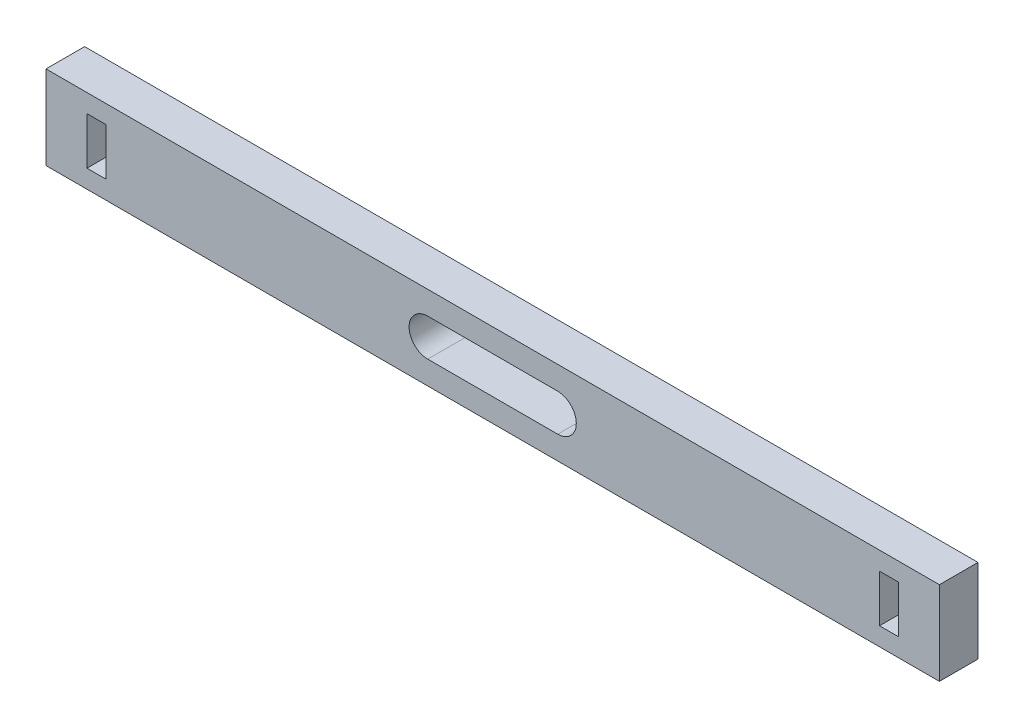
SolidWorks part; units mm, degrees
ref_plane "정면" through (0, 0, 0) normal (0, 0, 1) x (1, 0, 0)
ref_plane "윗면" through (0, 0, 0) normal (0, 1, 0) x (1, 0, 0)
ref_plane "우측면" through (0, 0, 0) normal (1, 0, 0) x (0, 0, -1)
sketch "Sketch1" plane through (0, 0, 0) normal (0, 0, 1) x (1, 0, 0)
  line L0 (-36.0327, -3.0341) -> (35.9673, -3.0341)
  line L1 (-36.0327, -3.0341) -> (-36.0327, 3.7149)
  line L2 (-36.0327, 3.7149) -> (35.9673, 3.7149)
  line L3 (35.9673, -3.0341) -> (35.9673, 3.7149)
  line L4 (31.1433, 2.2454) -> (31.1433, -1.5646)
  line L5 (32.6673, -1.5646) -> (31.1433, -1.5646)
  line L6 (-32.7327, 2.2454) -> (-31.2087, 2.2454)
  line L7 (-32.7327, 2.2454) -> (-32.7327, -1.5646)
  line L8 (-32.7327, -1.5646) -> (-31.2087, -1.5646)
  line L9 (-31.2087, 2.2454) -> (-31.2087, -1.5646)
  line L10 (32.6673, 2.2454) -> (32.6673, -1.5646)
  line L11 (32.6673, 2.2454) -> (31.1433, 2.2454)
  line L12 (-5.2701, 0.3404) -> (5.2047, 0.3404) construction
  line L13 (-5.2701, 1.8404) -> (5.2047, 1.8404)
  line L14 (-5.2701, -1.1596) -> (5.2047, -1.1596)
  line L15 (-0.0327, -3.0341) -> (-0.0327, 3.7149) construction
  line L16 (-36.0327, 0.3404) -> (35.9673, 0.3404) construction
  arc A0 (-5.2701, 1.8404) -> (-5.2701, -1.1596) centre (-5.2701, 0.3404) ccw
  arc A1 (5.2047, -1.1596) -> (5.2047, 1.8404) centre (5.2047, 0.3404) ccw
  point P15 (-0.0327, 0.3404)
  dimension "D1" = 72
  dimension "D2" = 3.3
  dimension "D3" = 3.3
extrude "Boss-Extrude1" add sketch "Sketch1" along normal blind 3.1115
